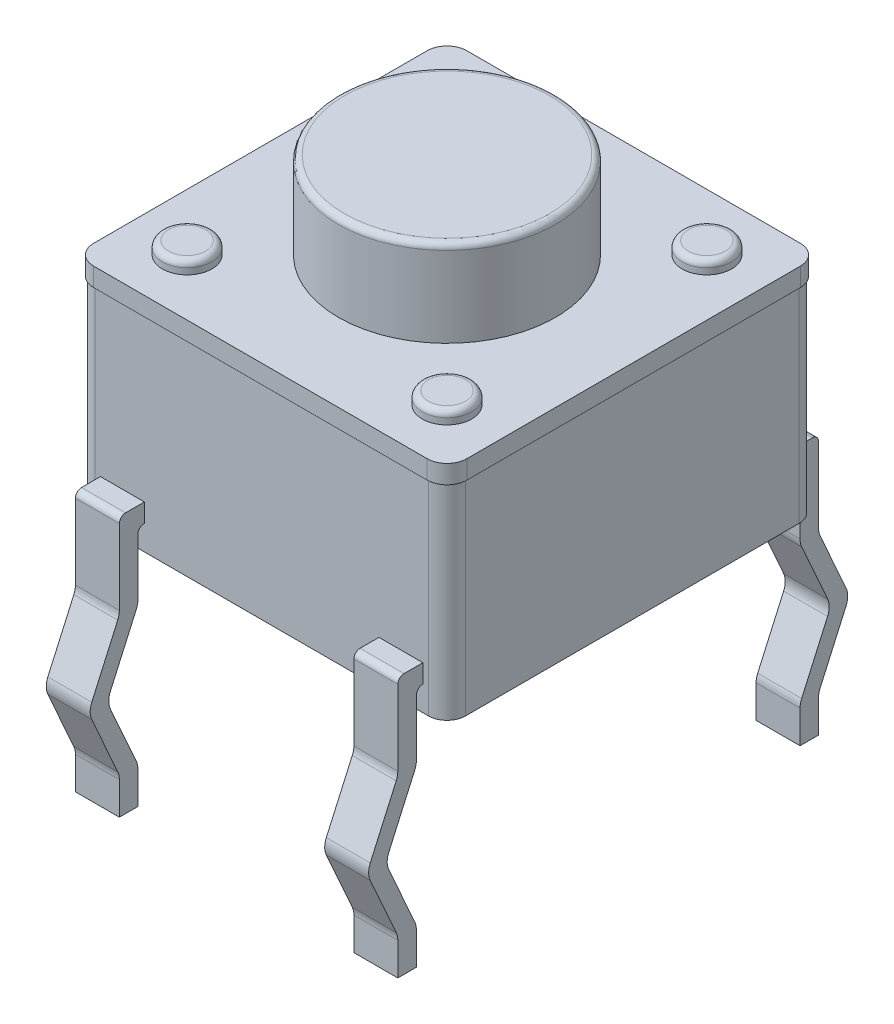
SolidWorks part; units mm, degrees
ref_plane "Plano frontal" through (0, 0, 0) normal (0, 0, 1) x (1, 0, 0)
ref_plane "Plano superior" through (0, 0, 0) normal (0, 1, 0) x (1, 0, 0)
ref_plane "Plano direito" through (0, 0, 0) normal (1, 0, 0) x (0, 0, -1)
sketch "Esboço1" plane through (0, 0, 0) normal (0, 1, 0) x (1, 0, 0)
  line L1 (-2.695, 2.995) -> (2.695, 2.995)
  line L2 (-2.995, 2.695) -> (-2.995, -2.695)
  line L3 (-2.695, -2.995) -> (2.695, -2.995)
  line L4 (2.995, 2.695) -> (2.995, -2.695)
  line L5 (-2.995, 2.995) -> (2.995, -2.995) construction
  line L6 (-2.995, -2.995) -> (2.995, 2.995) construction
  arc A0 (-2.995, -2.695) -> (-2.695, -2.995) centre (-2.695, -2.695) ccw
  arc A1 (2.695, -2.995) -> (2.995, -2.695) centre (2.695, -2.695) ccw
  arc A2 (2.695, 2.995) -> (2.995, 2.695) centre (2.695, 2.695) cw
  arc A3 (-2.695, 2.995) -> (-2.995, 2.695) centre (-2.695, 2.695) ccw
  point P0 (0, 0)
  dimension "D3" = 0.3
  dimension "D1" = 5.99
  dimension "D2" = 5.99
extrude "Ressalto-extrusão1" add sketch "Esboço1" along normal blind 3.61
sketch "Esboço2" plane through (0, 3.61, 0) normal (0, 1, 0) x (1, 0, 0)
  circle A0 centre (0, 0) radius 1.755
  dimension "D1" = 3.51
extrude "Ressalto-extrusão2" add sketch "Esboço2" along normal blind 1.4 separate body
fillet "Filete1" radius 0.1 1 edges at (0, 5.01, 1.755)
sketch "Esboço3" plane through (0, 3.61, 0) normal (0, 1, 0) x (1, 0, 0)
  line L0 (0, 0) -> (0, 2.995) construction
  line L1 (2.695, 2.995) -> (-2.695, 2.995) construction
  line L2 (0, 0) -> (-2.995, 0) construction
  line L3 (-2.995, 2.695) -> (-2.995, -2.695) construction
  circle A0 centre (-2.1, 2.1) radius 0.4
  circle A1 centre (2.1, 2.1) radius 0.4
  circle A2 centre (2.1, -2.1) radius 0.4
  circle A3 centre (-2.1, -2.1) radius 0.4
  dimension "D3" = 0.8
  dimension "D1" = 2.1
  dimension "D2" = 2.1
extrude "Ressalto-extrusão3" add sketch "Esboço3" along normal blind 0.2
fillet "Filete2" radius 0.1 4 edges at (2.1, 3.81, -2.5) (2.1, 3.81, 2.5) (-2.1, 3.81, -1.7) (-2.1, 3.81, 1.7)
sketch "Esboço4" plane through (0, 3.61, 0) normal (0, 1, 0) x (1, 0, 0)
  line L8 (-2.695, -3.015) -> (2.695, -3.015)
  line L9 (3.015, -2.695) -> (3.015, 2.695)
  line L10 (2.695, 3.015) -> (-2.695, 3.015)
  line L11 (-3.015, 2.695) -> (-3.015, -2.695)
  line L12 (-2.695, -3.015) -> (2.695, -3.015)
  line L13 (3.015, -2.695) -> (3.015, 2.695)
  line L14 (2.695, 3.015) -> (-2.695, 3.015)
  line L15 (-3.015, 2.695) -> (-3.015, -2.695)
  arc A8 (-3.015, -2.695) -> (-2.695, -3.015) centre (-2.695, -2.695) ccw
  arc A9 (2.695, -3.015) -> (3.015, -2.695) centre (2.695, -2.695) ccw
  arc A10 (3.015, 2.695) -> (2.695, 3.015) centre (2.695, 2.695) ccw
  arc A11 (-2.695, 3.015) -> (-3.015, 2.695) centre (-2.695, 2.695) ccw
  arc A12 (-3.015, -2.695) -> (-2.695, -3.015) centre (-2.695, -2.695) ccw
  arc A13 (2.695, -3.015) -> (3.015, -2.695) centre (2.695, -2.695) ccw
  arc A14 (3.015, 2.695) -> (2.695, 3.015) centre (2.695, 2.695) ccw
  arc A15 (-2.695, 3.015) -> (-3.015, 2.695) centre (-2.695, 2.695) ccw
  dimension "D1" = 0.02
extrude "Ressalto-extrusão4" add sketch "Esboço4" against normal blind 0.3
ref_plane "Plano1" through (2.25, 0, 0) normal (1, 0, 0) x (0, 0, -1)
sketch "Esboço5" plane through (2.25, 0, 0) normal (1, 0, 0) x (0, 0, -1)
  line L0 (3.25, -3.51) -> (3.25, 5.3695) construction
  line L1 (2.995, 0.4) -> (3, 0.4)
  line L2 (2.995, 3.31) -> (2.995, 0) construction
  line L3 (3.1, 0.3) -> (3.1, -0.6161)
  line L4 (3.1261, -0.7384) -> (3.5454, -1.6777)
  line L5 (3.5454, -1.9223) -> (3.1261, -2.8616)
  line L6 (3.1, -2.9839) -> (3.1, -3.51)
  line L7 (2.995, 0.7) -> (3.3, 0.7)
  line L8 (3.4, 0.6) -> (3.4, -0.6161)
  line L9 (3.4261, -0.7384) -> (3.8454, -1.6777)
  line L10 (3.8454, -1.9223) -> (3.4261, -2.8616)
  line L11 (3.4, -2.9839) -> (3.4, -3.51)
  line L12 (3.4, -3.51) -> (3.1, -3.51)
  line L13 (2.695, 0) -> (2.995, 0) construction
  line L14 (-2.695, 0) -> (2.695, 0) construction
  line L15 (2.995, 0.4) -> (2.995, 0.7)
  arc A0 (3.1261, -2.8616) -> (3.1, -2.9839) centre (3.4, -2.9839) ccw
  arc A1 (3.4261, -2.8616) -> (3.4, -2.9839) centre (3.7, -2.9839) ccw
  arc A2 (3.5454, -1.6777) -> (3.5454, -1.9223) centre (3.2715, -1.8) cw
  arc A3 (3.8454, -1.6777) -> (3.8454, -1.9223) centre (3.5715, -1.8) cw
  arc A4 (3.4, -0.6161) -> (3.4261, -0.7384) centre (3.7, -0.6161) ccw
  arc A5 (3.1, -0.6161) -> (3.1261, -0.7384) centre (3.4, -0.6161) ccw
  arc A6 (3.3, 0.7) -> (3.4, 0.6) centre (3.3, 0.6) cw
  arc A7 (3, 0.4) -> (3.1, 0.3) centre (3, 0.3) cw
  point P28 (3.6, -1.8)
  point P31 (3.9, -1.8)
  point P34 (3.4, -0.68)
  dimension "D11" = 0.3
  dimension "D12" = 0.1
  dimension "D1" = 3.25
  dimension "D2" = 0.3
  dimension "D3" = 0.3
  dimension "D4" = 0.3
  dimension "D5" = 0.3
  dimension "D6" = 0.68
  dimension "D7" = 3.51
  dimension "D8" = 1.8
  dimension "D9" = 3.9
  dimension "D10" = 0.7
extrude "Ressalto-extrusão5" add sketch "Esboço5" along normal blind 0.355 and the other way blind 0.355
mirror "Espelhar1" about plane through (0, 0, 0) normal (1, 0, 0) of "Ressalto-extrusão5"
mirror "Espelhar2" about plane through (0, 0, 0) normal (0, 0, 1) of "Espelhar1", "Ressalto-extrusão5"
